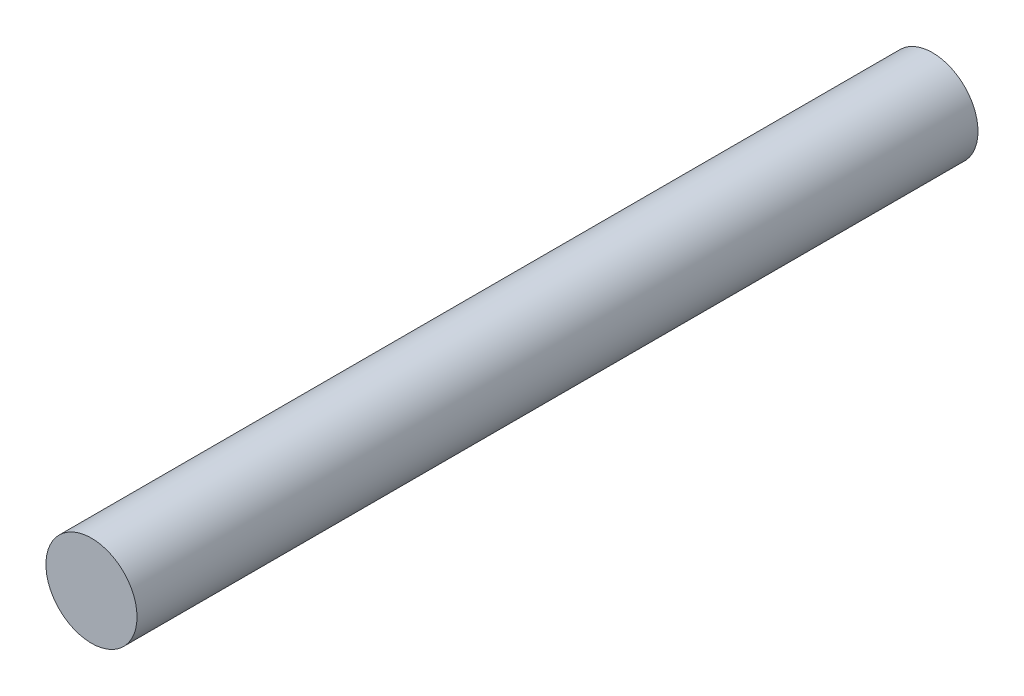
SolidWorks part; units mm, degrees
material "PA Type 6"
ref_plane "Front Plane" through (0, 0, 0) normal (0, 0, 1) x (1, 0, 0)
ref_plane "Top Plane" through (0, 0, 0) normal (0, 1, 0) x (1, 0, 0)
ref_plane "Right Plane" through (0, 0, 0) normal (1, 0, 0) x (0, 0, -1)
sketch "Sketch1" plane through (0, 0, 0) normal (0, 0, 1) x (1, 0, 0)
  circle A0 centre (0, 0) radius 6.5
  dimension "D1" = 13
extrude "Boss-Extrude1" add sketch "Sketch1" along normal mid plane 120
